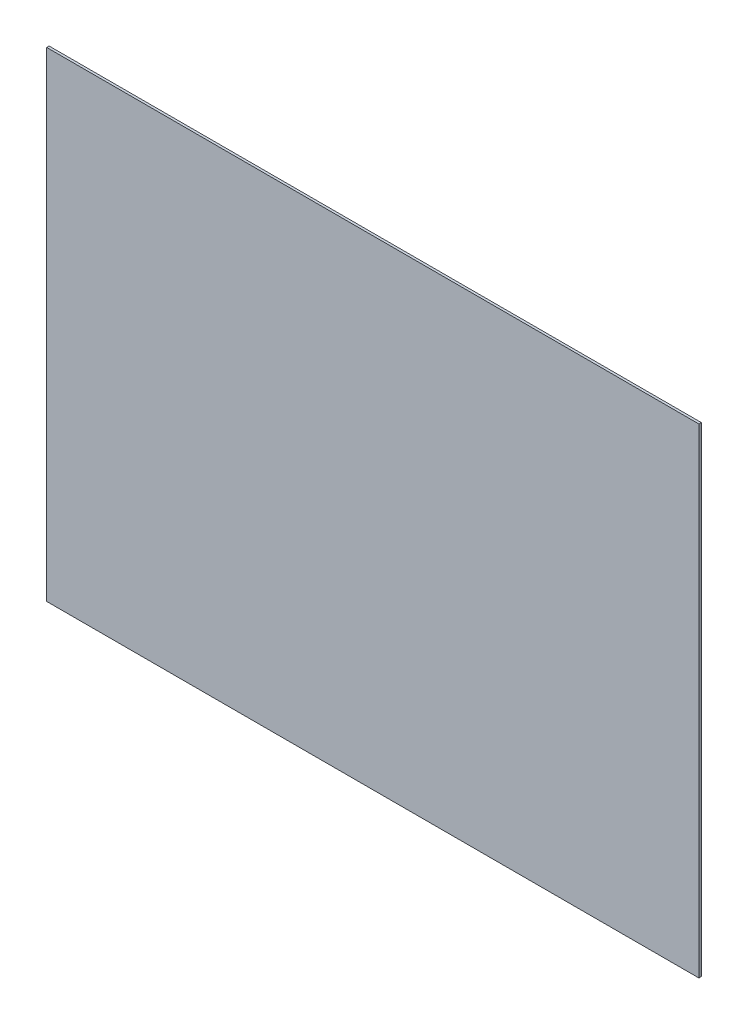
SolidWorks part; units mm, degrees
ref_plane "Front Plane" through (0, 0, 0) normal (0, 0, 1) x (1, 0, 0)
ref_plane "Top Plane" through (0, 0, 0) normal (0, 1, 0) x (1, 0, 0)
ref_plane "Right Plane" through (0, 0, 0) normal (1, 0, 0) x (0, 0, -1)
sketch "Sketch1" plane through (0, 0, 0) normal (0, 0, 1) x (1, 0, 0)
  line L1 (-5500, 6058) -> (7900, 6058)
  line L2 (-5500, 6058) -> (-5500, -3800)
  line L3 (-5500, -3800) -> (7900, -3800)
  line L4 (7900, 6058) -> (7900, -3800)
  dimension "D1" = 13400
  dimension "D2" = 7900
  dimension "D3" = 9858
  dimension "D4" = 3800
extrude "Extrude1" add sketch "Sketch1" against normal blind 50
